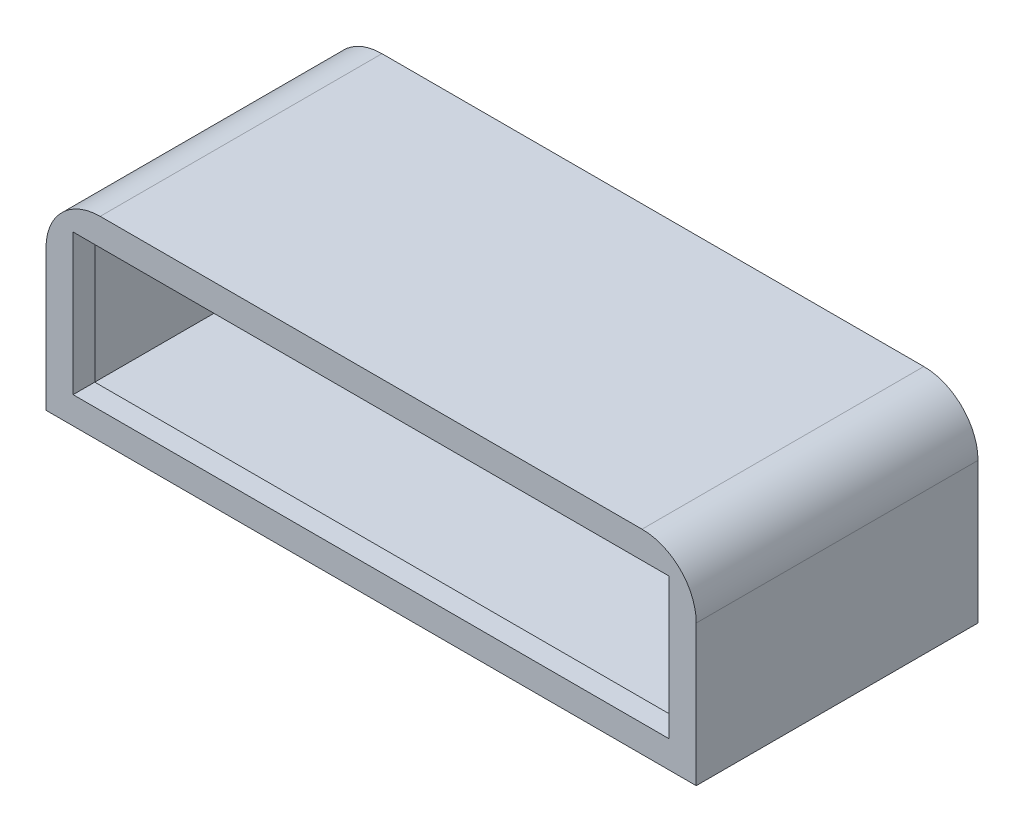
SolidWorks part; units mm, degrees
ref_plane "Front Plane" through (0, 0, 0) normal (0, 0, 1) x (1, 0, 0)
ref_plane "Top Plane" through (0, 0, 0) normal (0, 1, 0) x (1, 0, 0)
ref_plane "Right Plane" through (0, 0, 0) normal (1, 0, 0) x (0, 0, -1)
sketch "Sketch1" plane through (0, 0, 0) normal (0, 0, 1) x (1, 0, 0)
  line L1 (-76.2, -22.86) -> (76.2, -22.86)
  line L2 (-76.2, -22.86) -> (-76.2, 22.86)
  line L3 (-76.2, 22.86) -> (76.2, 22.86)
  line L4 (76.2, -22.86) -> (76.2, 22.86)
  line L5 (-76.2, -22.86) -> (76.2, 22.86) construction
  line L6 (-76.2, 22.86) -> (76.2, -22.86) construction
  point P0 (0, 0)
  dimension "D1" = 152.4
  dimension "D2" = 45.72
extrude "Boss-Extrude2" add sketch "Sketch1" along normal blind 66.04
sketch "Sketch2" plane through (0, 0, 66.04) normal (0, 0, 1) x (1, 0, 0)
  line L1 (-69.85, -16.51) -> (69.85, -16.51)
  line L2 (-69.85, -16.51) -> (-69.85, 16.51)
  line L3 (-69.85, 16.51) -> (69.85, 16.51)
  line L4 (69.85, -16.51) -> (69.85, 16.51)
  line L5 (-69.85, -16.51) -> (69.85, 16.51) construction
  line L6 (-69.85, 16.51) -> (69.85, -16.51) construction
  point P0 (0, 0)
  dimension "D1" = 139.7
  dimension "D2" = 33.02
shell "Shell1" thickness 5.08
extrude "Cut-Extrude1" cut sketch "Sketch2" against normal blind 13.462
fillet "Fillet1" radius 12.7 2 edges at (76.2, 22.86, 33.02) (-76.2, 22.86, 33.02)
sketch "Sketch4" plane through (0, 0, 0) normal (0, 0, -1) x (-1, 0, 0)
  line L0 (-76.2, -22.86) -> (-76.2, 10.16) construction
  line L1 (76.2, -22.86) -> (-76.2, -22.86) construction
  line L2 (36.322, 0) -> (-36.322, 0) construction
  line L3 (0, 25.146) -> (0, -25.146) construction
  circle A0 centre (-57.15, -20.32) radius 1
  circle A1 centre (-57.15, 20.32) radius 1
  circle A2 centre (57.15, 20.32) radius 1
  circle A3 centre (57.15, -20.32) radius 1
  dimension "D1" = 2
  dimension "D2" = 19.05
  dimension "D3" = 2.54
extrude "Cut-Extrude2" cut sketch "Sketch4" against normal blind 3.175
